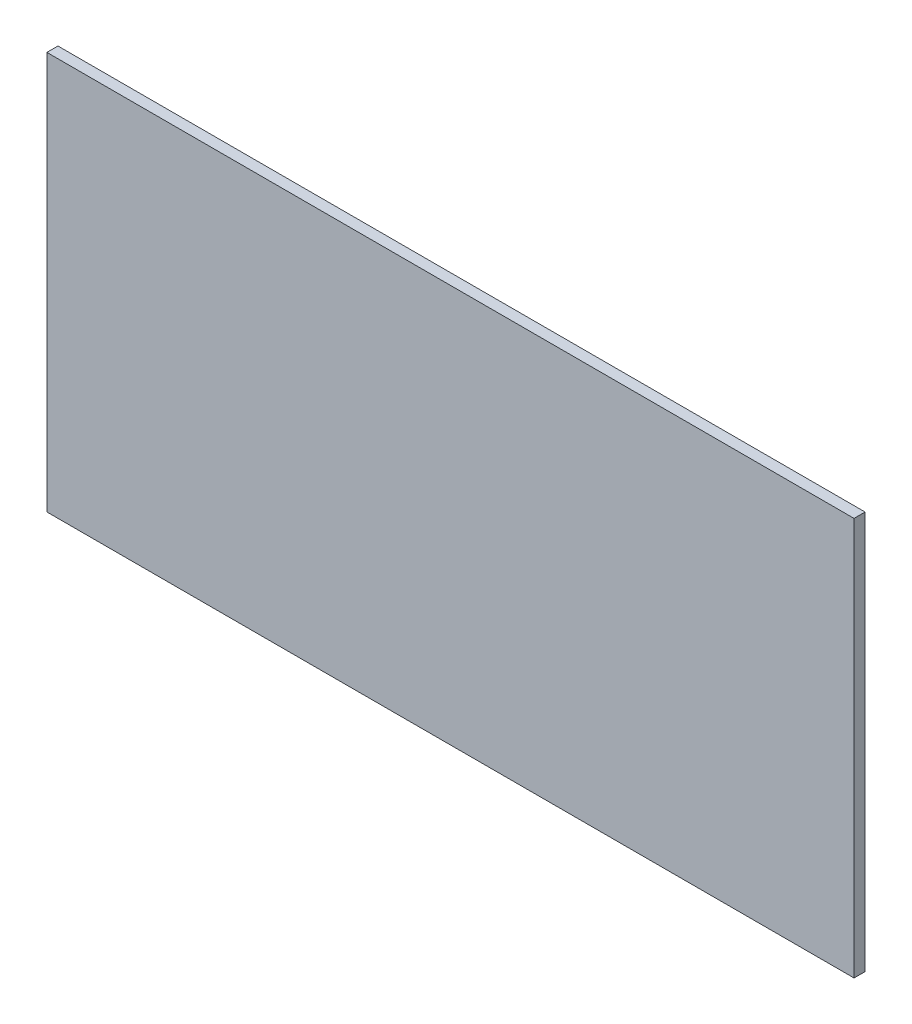
SolidWorks part; units mm, degrees
ref_plane "Front Plane" through (0, 0, 0) normal (0, 0, 1) x (1, 0, 0)
ref_plane "Top Plane" through (0, 0, 0) normal (0, 1, 0) x (1, 0, 0)
ref_plane "Right Plane" through (0, 0, 0) normal (1, 0, 0) x (0, 0, -1)
sketch "Sketch1" plane through (0, 0, 0) normal (0, 0, 1) x (1, 0, 0)
  line L1 (-3.65, 1.8) -> (69.35, 1.8)
  line L2 (-3.65, 1.8) -> (-3.65, -34.2)
  line L3 (-3.65, -34.2) -> (69.35, -34.2)
  line L4 (69.35, 1.8) -> (69.35, -34.2)
  point P0 (0, 0)
  point P6 (0, 0)
  dimension "Length" = 73
  dimension "Height " = 36
extrude "Boss-Extrude1" add sketch "Sketch1" along normal blind 1
sketch "Sketch2" plane through (0, 0, 1) normal (0, 0, 1) x (1, 0, 0)
  line L1 (4.35, -0.2) -> (67.35, -0.2)
  line L2 (4.35, -0.2) -> (4.35, -32.2)
  line L3 (4.35, -32.2) -> (67.35, -32.2)
  line L4 (69.35, -34.2) -> (69.35, 1.8)
  line L5 (69.35, 1.8) -> (-3.65, 1.8)
  line L6 (-3.65, 1.8) -> (-3.65, -34.2)
  line L7 (-3.65, -34.2) -> (69.35, -34.2)
  line L8 (69.35, -34.2) -> (69.35, 1.8)
  line L9 (69.35, 1.8) -> (-3.65, 1.8)
  line L10 (-3.65, 1.8) -> (-3.65, -34.2)
  line L11 (-3.65, -34.2) -> (69.35, -34.2)
  line L12 (67.35, -0.2) -> (67.35, -32.2)
  text T0 "<b>Hello!</b>\r\n<b>Ali Badshah</b>\r\n<b>RSC</b>" font "Century Gothic" height 3.5
  point P2 (35.85, -16.2)
  dimension "D2" = 2
  dimension "D3" = 8
  dimension "D4" = 2
  dimension "D5" = 32
  dimension "D1" = 0
